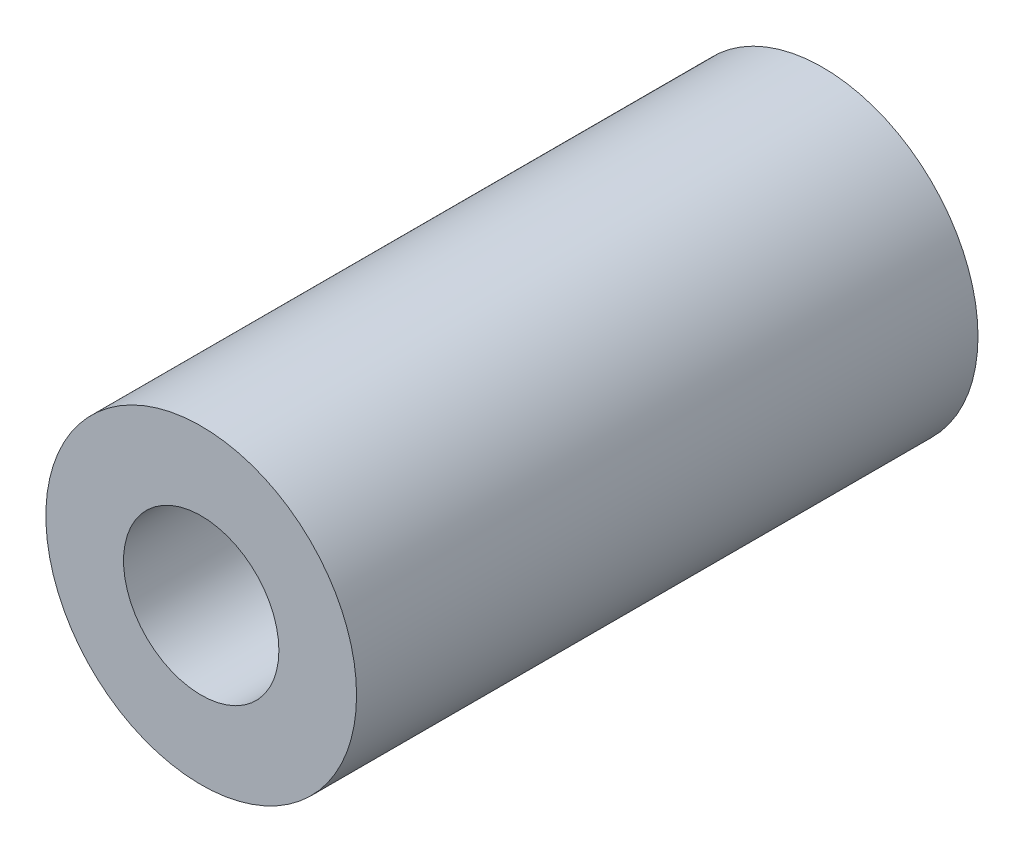
SolidWorks part; units mm, degrees
material "Nylon 6/10"
ref_plane "Front Plane" through (0, 0, 0) normal (0, 0, 1) x (1, 0, 0)
ref_plane "Top Plane" through (0, 0, 0) normal (0, 1, 0) x (1, 0, 0)
ref_plane "Right Plane" through (0, 0, 0) normal (1, 0, 0) x (0, 0, -1)
sketch "Sketch1" plane through (0, 0, 0) normal (0, 0, 1) x (1, 0, 0)
  circle A0 centre (0, 0) radius 1.5
  circle A1 centre (0, 0) radius 3
  dimension "D1" = 6
  dimension "D2" = 3
extrude "Boss-Extrude1" add sketch "Sketch1" along normal blind 12
